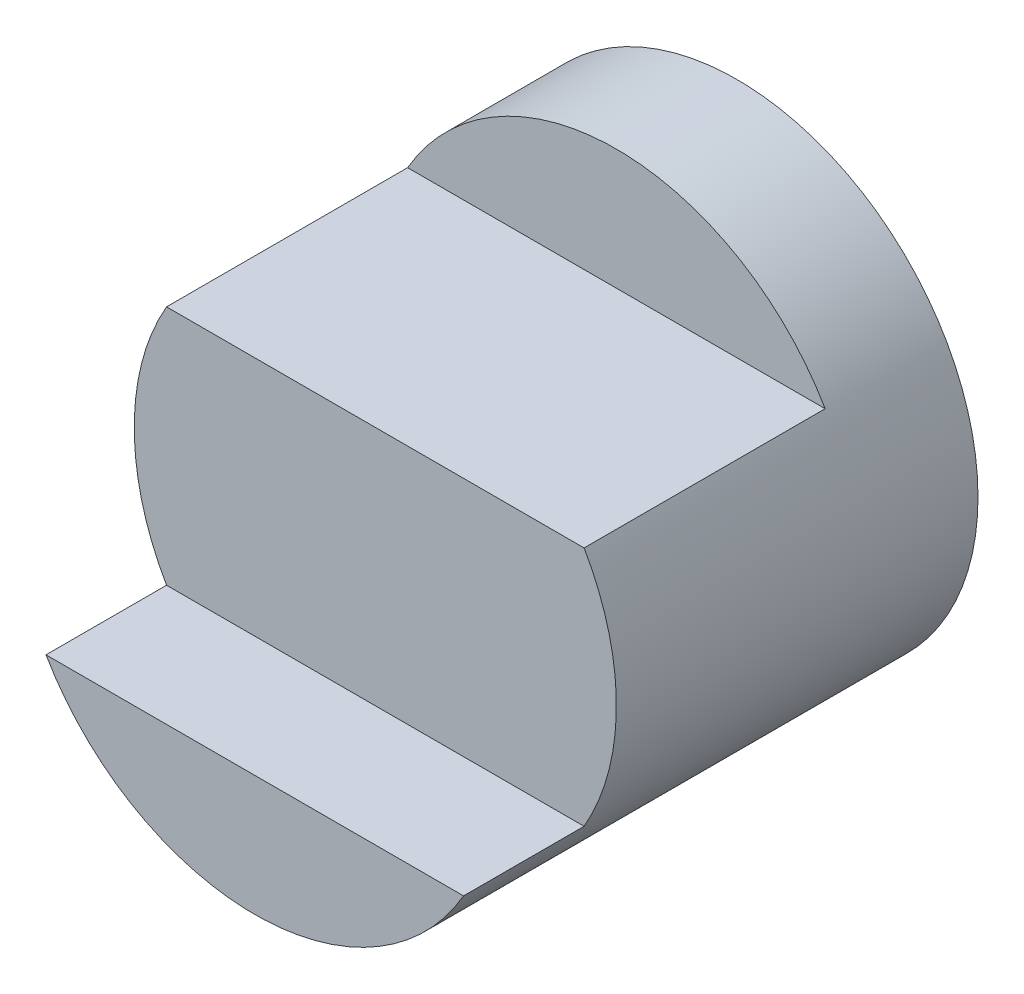
SolidWorks part; units mm, degrees
ref_plane "Front" through (0, 0, 0) normal (0, 0, 1) x (1, 0, 0)
ref_plane "Top" through (0, 0, 0) normal (0, 1, 0) x (1, 0, 0)
ref_plane "Right" through (0, 0, 0) normal (1, 0, 0) x (0, 0, -1)
sketch "Sketch1" plane through (0, 0, 0) normal (0, 0, 1) x (1, 0, 0)
  circle A0 centre (0, 0) radius 2
  dimension "D1" = 4
extrude "Boss-Extrude1" add sketch "Sketch1" along normal blind 4
sketch "Sketch2" plane through (0, 0, 4) normal (0, 0, 1) x (1, 0, 0)
  line L1 (-1.7321, -1) -> (1.7321, -1)
  circle A0 centre (0, 0) radius 2 construction
  arc A2 (-1.7321, -1) -> (1.7321, -1) centre (0, 0) ccw
  dimension "D1" = 1
extrude "Boss-Extrude2" add sketch "Sketch2" along normal blind 1
sketch "Sketch3" plane through (0, 0, 4) normal (0, 0, 1) x (1, 0, 0)
  line L0 (-1.7321, 1) -> (1.7321, 1)
  arc A0 (1.7321, -1) -> (-1.7321, -1) centre (0, 0) ccw construction
  arc A1 (-1.7321, 1) -> (1.7321, 1) centre (0, 0) cw
  dimension "D1" = 1
extrude "Cut-Extrude1" cut sketch "Sketch3" against normal blind 3
sketch "Sketch4" plane through (0, 0, 0) normal (1, 0, 0) x (0, 0, -1)
  line L0 (-4, -1) -> (-3, -1)
  line L1 (-3, -1) -> (-3, 1)
  line L2 (-1, 1) -> (-4, 1) construction
  line L3 (-3, 1) -> (-3, 1.7578)
  line L4 (-3, 1.7578) -> (-5.7636, 1.8063)
  line L5 (-5.7636, 1.8063) -> (-6.0329, -1.9754)
  line L6 (-6.0329, -1.9754) -> (-4.3414, -2.2448)
  line L7 (-4.3414, -2.2448) -> (-4, -2.2448)
  line L8 (-4, -2.2448) -> (-4, -1)
  line L9 (-4, 1) -> (-4, -1) construction
  dimension "D1" = 1
extrude "Cut-Extrude2" cut sketch "Sketch4" against normal mid plane 12
